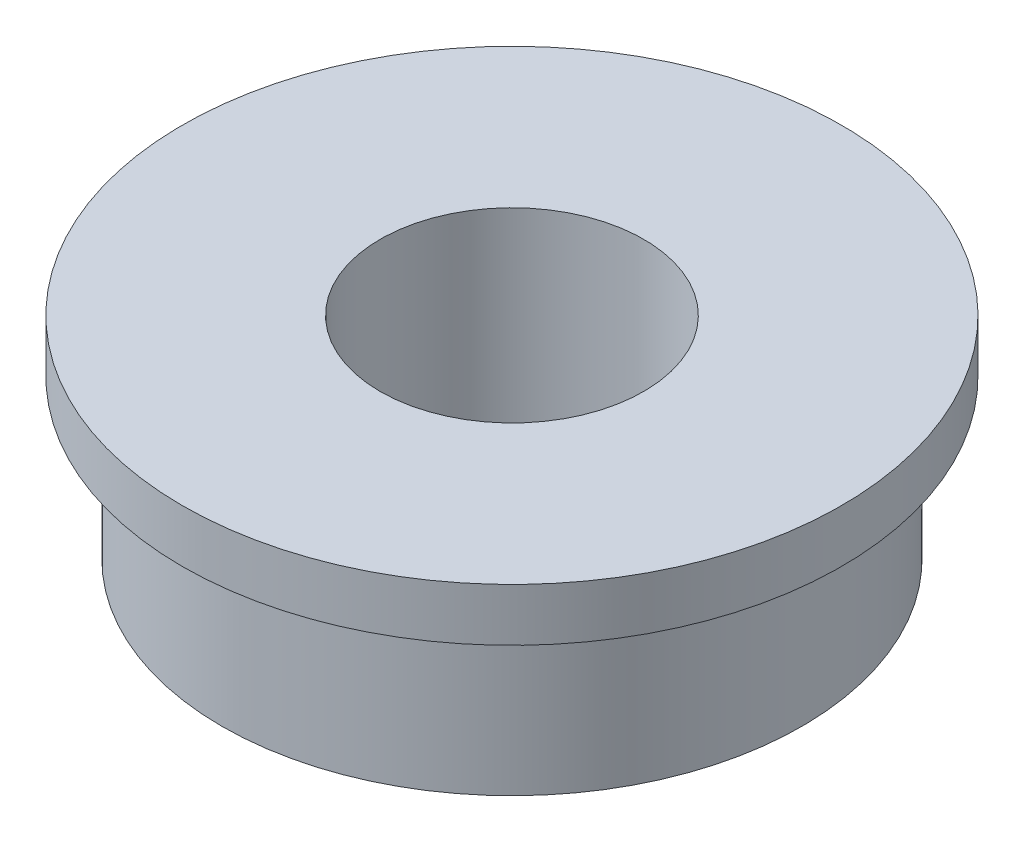
SolidWorks part; units mm, degrees
ref_plane "Front" through (0, 0, 0) normal (0, 0, 1) x (1, 0, 0)
ref_plane "Top" through (0, 0, 0) normal (0, 1, 0) x (1, 0, 0)
ref_plane "Right" through (0, 0, 0) normal (1, 0, 0) x (0, 0, -1)
sketch "Sketch1" plane through (0, 0, 0) normal (1, 0, 0) x (0, 0, -1)
  line L0 (2.5, 0) -> (5.5, 0)
  line L1 (5.5, 0) -> (5.5, 3)
  line L2 (5.5, 3) -> (6.25, 3)
  line L3 (6.25, 3) -> (6.25, 4)
  line L4 (6.25, 4) -> (2.5, 4)
  line L5 (2.5, 4) -> (2.5, 0)
  line L6 (0, 9.3296) -> (0, -4.2458) construction
  dimension "D1" = 2.5
  dimension "D2" = 5.5
  dimension "D3" = 4
  dimension "D4" = 6.25
  dimension "D5" = 1
revolve "Revolve1" add sketch "Sketch1" angle 360 about L6
